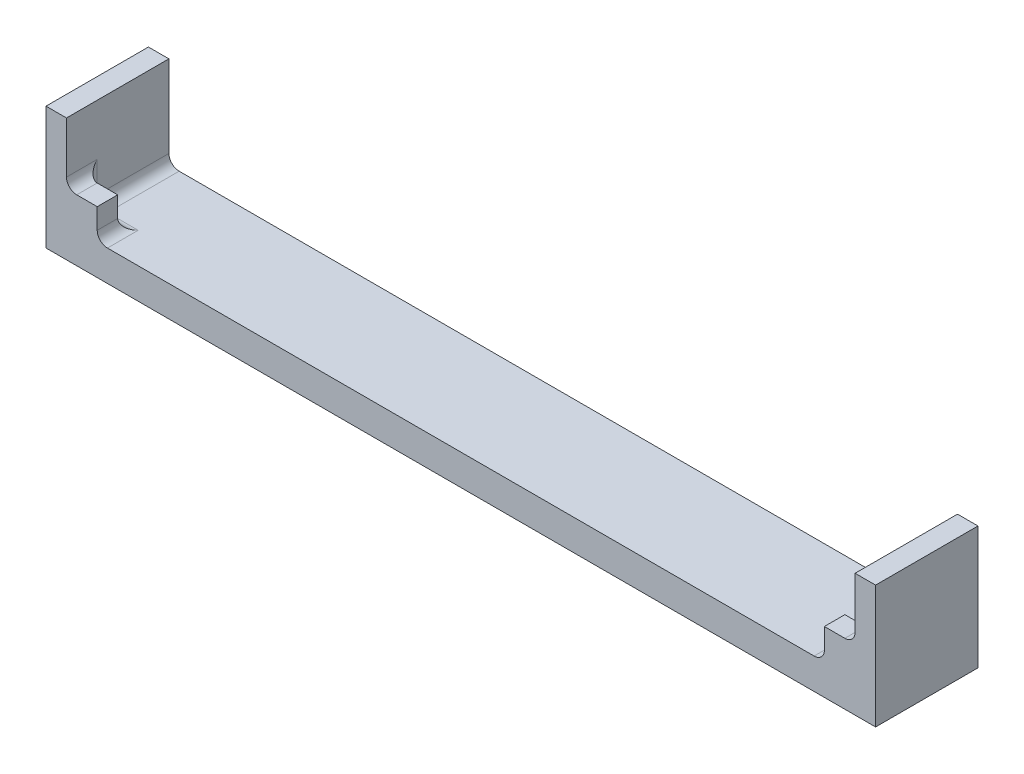
SolidWorks part; units mm, degrees
ref_plane "Front Plane" through (0, 0, 0) normal (0, 0, 1) x (1, 0, 0)
ref_plane "Top Plane" through (0, 0, 0) normal (0, 1, 0) x (1, 0, 0)
ref_plane "Right Plane" through (0, 0, 0) normal (1, 0, 0) x (0, 0, -1)
sketch "Sketch1" plane through (0, 0, 0) normal (0, 1, 0) x (1, 0, 0)
  line L1 (0, 0) -> (81, 0)
  line L2 (0, 0) -> (0, 10)
  line L3 (0, 10) -> (81, 10)
  line L4 (81, 0) -> (81, 10)
  dimension "D1" = 81
  dimension "D2" = 10
extrude "Boss-Extrude1" add sketch "Sketch1" along normal blind 3
sketch "Sketch2" plane through (0, 3, 0) normal (0, 1, 0) x (1, 0, 0)
  line L0 (0, 0) -> (81, 0) construction
  line L1 (0, 10) -> (2, 10)
  line L2 (0, 10) -> (0, 0)
  line L3 (0, 0) -> (2, 0)
  line L4 (2, 10) -> (2, 0)
  line L6 (81, 10) -> (79, 10)
  line L7 (81, 10) -> (81, 0)
  line L8 (81, 0) -> (79, 0)
  line L9 (79, 10) -> (79, 0)
  dimension "D1" = 2
  dimension "D2" = 2
extrude "Boss-Extrude2" add sketch "Sketch2" along normal blind 9
sketch "Sketch3" plane through (0, 0, 0) normal (0, 0, 1) x (1, 0, 0)
  line L1 (2, 3) -> (5, 3)
  line L2 (2, 3) -> (2, 6)
  line L3 (2, 6) -> (5, 6)
  line L4 (5, 3) -> (5, 6)
  line L5 (79, 3) -> (76, 3)
  line L6 (79, 3) -> (79, 6)
  line L7 (79, 6) -> (76, 6)
  line L8 (76, 3) -> (76, 6)
  dimension "D1" = 3
  dimension "D2" = 3
  dimension "D3" = 3
  dimension "D4" = 3
extrude "Boss-Extrude3" add sketch "Sketch3" against normal blind 2
fillet "Fillet1" radius 1 2 edges at (2, 3, -6) (79, 3, -6)
fillet "Fillet2" radius 1 10 edges at (77, 3, -2) (78.7071, 3.2929, -2) (4, 3, -2) (2.2929, 3.2929, -2) (76, 3, -1) (79, 5, -2) (79, 6, -1) (2, 6, -1) (5, 3, -1) (2, 5, -2)
